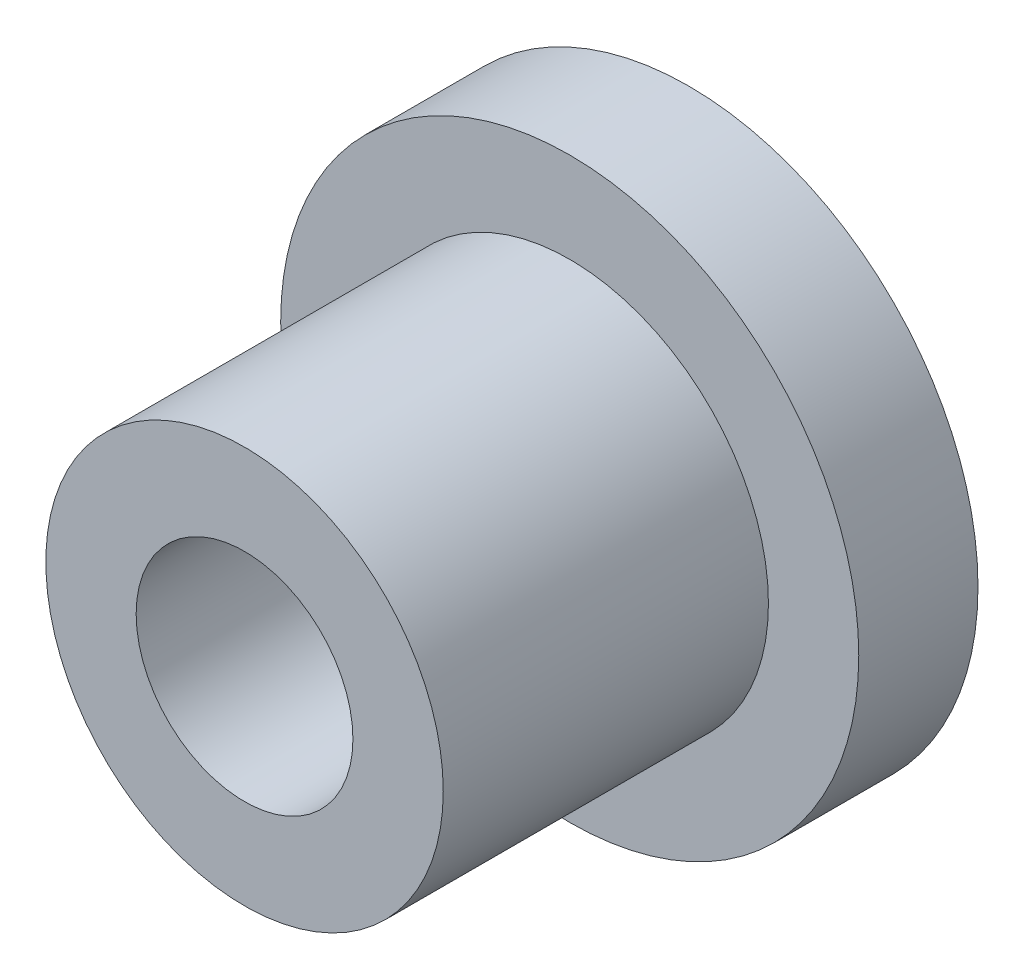
SolidWorks part; units mm, degrees
ref_plane "Front Plane" through (0, 0, 0) normal (0, 0, 1) x (1, 0, 0)
ref_plane "Top Plane" through (0, 0, 0) normal (0, 1, 0) x (1, 0, 0)
ref_plane "Right Plane" through (0, 0, 0) normal (1, 0, 0) x (0, 0, -1)
sketch "Sketch1" plane through (0, 0, 0) normal (1, 0, 0) x (0, 0, -1)
  line L0 (0, 0) -> (21.6221, 0) construction
  line L1 (0, 3) -> (9, 3)
  line L2 (9, 3) -> (12.3, 6.3)
  line L3 (12.3, 6.3) -> (12.3, 8)
  line L4 (12.3, 8) -> (9, 8)
  line L5 (9, 8) -> (9, 5.5)
  line L6 (9, 5.5) -> (0, 5.5)
  line L7 (0, 5.5) -> (0, 3)
  dimension "D1" = 3.3
  dimension "D2" = 9
  dimension "D3" = 8
  dimension "D4" = 135
  dimension "D5" = 3
  dimension "D6" = 5.5
revolve "Revolve1" add sketch "Sketch1" angle 360 about L0
